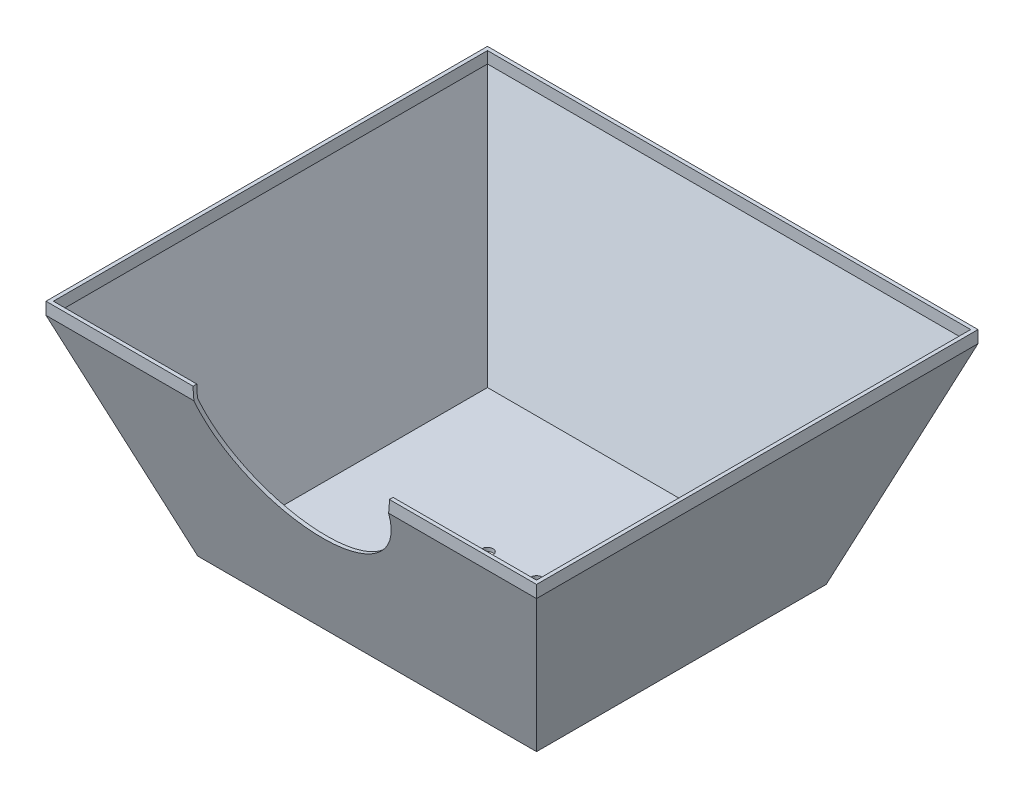
SolidWorks part; units mm, degrees
ref_plane "Front Plane" through (0, 0, 0) normal (0, 0, 1) x (1, 0, 0)
ref_plane "Top Plane" through (0, 0, 0) normal (0, 1, 0) x (1, 0, 0)
ref_plane "Right Plane" through (0, 0, 0) normal (1, 0, 0) x (0, 0, -1)
sketch "Sketch1" plane through (0, 0, 0) normal (0, 1, 0) x (1, 0, 0)
  line L1 (0, 0) -> (200, 0)
  line L2 (0, 0) -> (0, 180)
  line L3 (0, 180) -> (200, 180)
  line L4 (200, 0) -> (200, 180)
  dimension "D1" = 200
  dimension "D2" = 180
extrude "Boss-Extrude1" add sketch "Sketch1" along normal blind 90
sketch "Sketch4" plane through (0, 0, 0) normal (0, 0, 1) x (1, 0, 0)
  line L0 (0, 85) -> (30.9375, 0)
  line L1 (0, 90) -> (0, 0) construction
  line L2 (0, 0) -> (200, 0) construction
  line L3 (100, 90) -> (100, 0) construction
  line L4 (0, 90) -> (200, 90) construction
  line L5 (0, 85) -> (0, 0)
  line L6 (0, 0) -> (30.9375, 0)
  line L7 (200, 85) -> (200, 0)
  line L8 (200, 85) -> (169.0625, 0)
  line L9 (200, 0) -> (169.0625, 0)
  dimension "D1" = 5
  dimension "D2" = 70
extrude "Cut-Extrude1" cut sketch "Sketch4" against normal through all and the other way through all contours L6 L0 L5 | L7 L9 L8
sketch "Sketch5" plane through (0, 0, 0) normal (-1, 0, 0) x (0, 0, 1)
  line L0 (-180, 85) -> (-149.0625, 0)
  line L1 (-180, 85) -> (-180, 0) construction
  line L2 (-180, 0) -> (0, 0) construction
  line L3 (-90, 90) -> (-90, 0) construction
  line L4 (-180, 90) -> (0, 90) construction
  line L5 (-180, 85) -> (-180, 0)
  line L6 (-180, 0) -> (-149.0625, 0)
  line L7 (0, 85) -> (-30.9375, 0)
  line L8 (0, 85) -> (0, 0)
  line L9 (0, 0) -> (-30.9375, 0)
  dimension "D1" = 5
  dimension "D2" = 70
extrude "Cut-Extrude2" cut sketch "Sketch5" against normal through all contours L6 L0 L5 | L7 L9 L8
shell "Shell1" thickness 1.5
sketch "Sketch6" plane through (0, 1.5, 0) normal (0, 1, 0) x (1, 0, 0)
  line L0 (168.0122, 148.0122) -> (168.0122, 31.9878) construction
  line L1 (168.0122, 31.9878) -> (31.9878, 31.9878) construction
  line L2 (31.9878, 148.0122) -> (31.9878, 31.9878) construction
  line L3 (168.0122, 148.0122) -> (31.9878, 148.0122) construction
  line L4 (168.0122, 148.0122) -> (168.0122, 31.9878)
  line L5 (168.0122, 31.9878) -> (31.9878, 31.9878)
  line L6 (31.9878, 148.0122) -> (31.9878, 31.9878)
  line L7 (168.0122, 148.0122) -> (31.9878, 148.0122)
  line L8 (31.9878, 90) -> (168.0122, 90) construction
  line L9 (100, 148.0122) -> (100, 31.9878) construction
  circle A0 centre (90, 90) radius 2.25
  circle A2 centre (110, 90) radius 2.25
  point P11 (100, 90)
  point P13 (100, 90)
  dimension "D2" = 4.5
  dimension "D1" = 10
extrude "Hinge-Holes" cut sketch "Sketch6" against normal through all contours A0 | A2
sketch "Sketch7" plane through (0, 0, 0) normal (0, 0, 1) x (1, 0, 0)
  line L0 (0, 90) -> (200, 90) construction
  line L1 (0, 90) -> (200, 90)
  line L2 (60, 90) -> (140, 90)
  arc A0 (60, 90) -> (140, 90) centre (100, 90) ccw
  point P6 (100, 90)
  line M2 (0, 85) -> (200, 85)
  dimension "D1" = 40
extrude "Cut-Extrude4" cut sketch "Sketch7" against normal blind 50 contours A0 M2 | L1 A0 M2
ref_plane "Plane1" through (0, 40, 0) normal (0, 1, 0) x (1, 0, 0)
